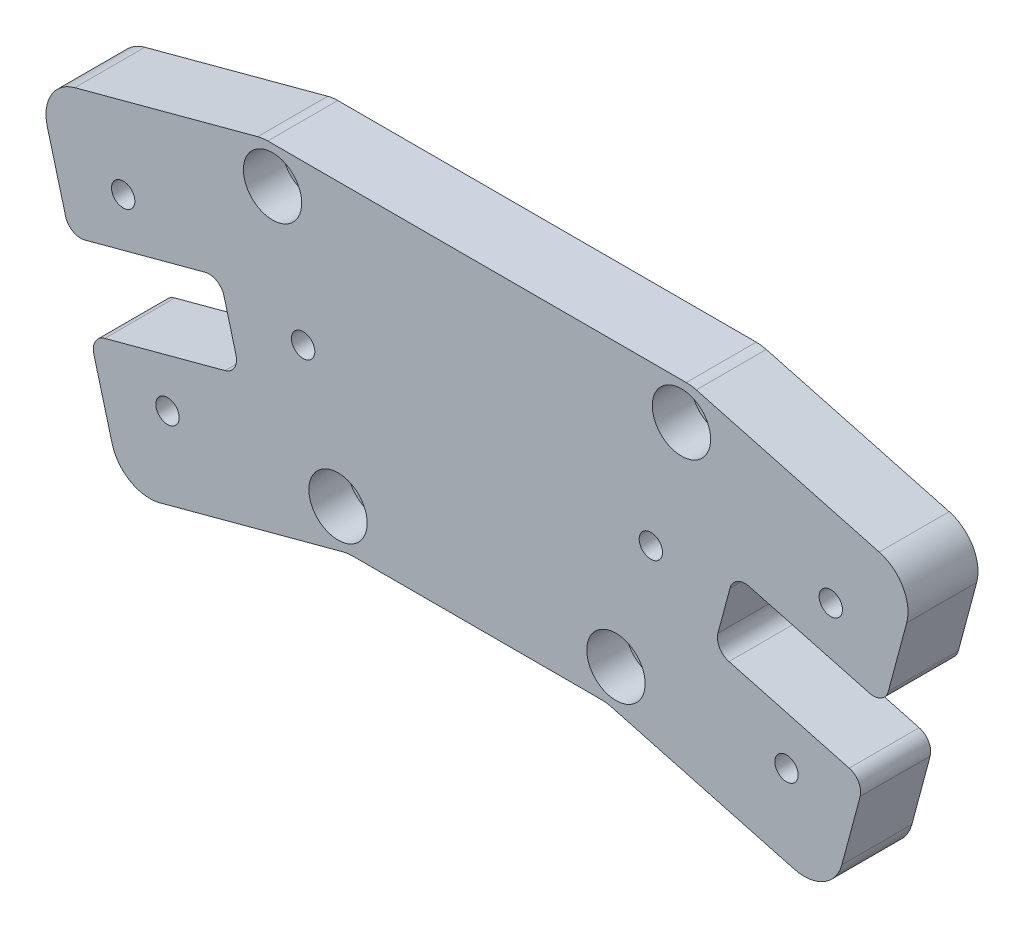
SolidWorks part; units mm, degrees
material "ABS"
ref_plane "前视基准面" through (0, 0, 0) normal (0, 0, 1) x (1, 0, 0)
ref_plane "上视基准面" through (0, 0, 0) normal (0, 1, 0) x (1, 0, 0)
ref_plane "右视基准面" through (0, 0, 0) normal (1, 0, 0) x (0, 0, -1)
other "Configuration Table"
sketch "草图1" plane through (0, 0, 0) normal (0, 0, 1) x (1, 0, 0)
  line L0 (-27.5552, 0) -> (27.5552, 0)
  line L4 (16.6342, -40.7579) -> (-16.6342, -40.7579)
  line L8 (0, 0) -> (0, -40.7579) construction
  line L9 (-45.612, -48.5224) -> (-16.6342, -40.7579)
  line L10 (-56.533, -7.7646) -> (-52.3666, -23.3139)
  line L11 (-27.5552, 0) -> (-56.533, -7.7646)
  line L12 (-60, -30.6224) -> (-60, 11.8776) construction
  line L13 (-60, -30.6224) -> (-85.8724, 3.0952) construction
  line L14 (-60, -30.6224) -> (-17.5, -30.6224) construction
  line L15 (-60, -30.6224) -> (-34.1276, -64.3399) construction
  line L16 (-27.5552, 0) -> (-16.6342, -40.7579) construction
  line L17 (-60.0552, -30.5504) -> (-22.0947, -20.3789) construction
  line L18 (-52.3666, -23.3139) -> (-33.0481, -18.1375)
  line L19 (-52.8305, -11.0149) -> (-44.0307, -43.8563) construction
  line L20 (-49.7784, -32.9731) -> (-30.4599, -27.7968)
  line L27 (-33.0481, -18.1375) -> (-30.4599, -27.7968)
  line L30 (-49.7784, -32.9731) -> (-45.612, -48.5224)
  line L31 (27.5552, 0) -> (56.533, -7.7646)
  line L32 (56.533, -7.7646) -> (52.3666, -23.3139)
  line L33 (52.3666, -23.3139) -> (33.0481, -18.1375)
  line L38 (33.0481, -18.1375) -> (30.4599, -27.7968)
  line L43 (49.7784, -32.9731) -> (30.4599, -27.7968)
  line L44 (49.7784, -32.9731) -> (45.612, -48.5224)
  line L45 (45.612, -48.5224) -> (16.6342, -40.7579)
  line L46 (-52.8305, -11.0149) -> (-45.1031, -8.9443) construction
  line L47 (-45.1031, -8.9443) -> (-18.815, -14.3238) construction
  line L48 (-18.815, -14.3238) -> (-16.2269, -23.983) construction
  line L49 (-17.5209, -19.1534) -> (-22.0947, -20.3789) construction
  line L50 (-44.0307, -43.8563) -> (-36.3032, -41.7858) construction
  line L51 (-36.3032, -41.7858) -> (-16.2269, -23.983) construction
  line L52 (-45.482, -15.2575) -> (-39.788, -36.5079) construction
  circle A0 centre (-60, -30.6224) radius 42.5 construction
  circle A1 centre (-85.8724, 3.0952) radius 1.75 construction
  circle A2 centre (-54.4526, 11.514) radius 1.75 construction
  circle A3 centre (-26.2825, -4.75) radius 1.75
  circle A4 centre (-17.8636, -36.1697) radius 1.75
  circle A5 centre (-34.1276, -64.3399) radius 1.75 construction
  circle A6 centre (-65.5474, -72.7588) radius 1.75 construction
  circle A7 centre (-93.7175, -56.4947) radius 1.75 construction
  circle A8 centre (-102.1364, -25.075) radius 1.75 construction
  circle A9 centre (-26.2825, -4.75) radius 3.75 construction
  circle A11 centre (-17.8636, -36.1697) radius 3.75 construction
  circle A12 centre (-26.2825, -4.75) radius 4.75 construction
  circle A13 centre (-17.8636, -36.1697) radius 4.75 construction
  circle A14 centre (17.8636, -36.1697) radius 1.75
  circle A15 centre (26.2825, -4.75) radius 1.75
  circle A16 centre (60, -30.6224) radius 42.5 construction
  circle A17 centre (-45.482, -15.2575) radius 1.5
  circle A18 centre (-22.3506, -20.4475) radius 1.5
  circle A19 centre (-39.788, -36.5079) radius 1.5
  circle A20 centre (45.482, -15.2575) radius 1.5
  circle A21 centre (39.788, -36.5079) radius 1.5
  circle A22 centre (22.3506, -20.4475) radius 1.5
  point P31 (-60, -30.6224)
  point P45 (-48.4306, -27.4356)
  dimension "D6" = 85
  dimension "D9" = 3.5
  dimension "D10" = 7.5
  dimension "D14" = 1
  dimension "D4" = 1
  dimension "D12" = 12
  dimension "D19" = 22
  dimension "D20" = 3
  dimension "D21" = 5
  dimension "D2" = 120
  dimension "D3" = 10
  dimension "D5" = 30
  dimension "D7" = 37.5
  dimension "D11" = 20
  dimension "D13" = 8
  dimension "D15" = 10
  dimension "D16" = 32
  dimension "D17" = 34
  dimension "D18" = 6
  dimension "D8" = 8
extrude "凸台-拉伸1" add sketch "草图1" along normal blind 9 contours L0 L31 L32 L33 L38 L43 L44 L45 L4 L9 L30 L20 L27 L18 L10 L11
fillet "圆角1" radius 5 8 edges at (27.5552, 0, 4.5) (56.533, -7.7646, 4.5) (16.6342, -40.7579, 4.5) (45.612, -48.5224, 4.5) (-45.612, -48.5224, 4.5) (-16.6342, -40.7579, 4.5) (-27.5552, 0, 4.5) (-56.533, -7.7646, 4.5)
sketch "草图2" plane through (0, 0, 0) normal (0, 0, -1) x (-1, 0, 0)
  line L0 (-45.482, -15.2575) -> (-22.3506, -20.4475) construction
  line L1 (-42.3033, -14.4058) -> (-44.6303, -12.0787)
  line L2 (-44.6303, -12.0787) -> (-47.809, -12.9305)
  line L3 (-47.809, -12.9305) -> (-48.6608, -16.1093)
  line L4 (-48.6608, -16.1093) -> (-46.3338, -18.4363)
  line L5 (-46.3338, -18.4363) -> (-43.155, -17.5845)
  line L6 (-43.155, -17.5845) -> (-42.3033, -14.4058)
  line L7 (-22.3506, -20.4475) -> (-39.788, -36.5079) construction
  line L8 (-39.788, -36.5079) -> (-45.482, -15.2575) construction
  line L9 (-30.4599, -27.7968) -> (-33.0481, -18.1375) construction
  line L10 (-31.754, -22.9671) -> (-22.3506, -20.4475) construction
  line L11 (-33.0481, -18.1375) -> (-52.3666, -23.3139) construction
  line L12 (0, 0) -> (0, -40.7579) construction
  line L13 (-21.4988, -23.6263) -> (-19.1718, -21.2992)
  line L14 (-19.1718, -21.2992) -> (-20.0236, -18.1205)
  line L15 (-20.0236, -18.1205) -> (-23.2023, -17.2687)
  line L16 (-23.2023, -17.2687) -> (-25.5293, -19.5957)
  line L17 (-25.5293, -19.5957) -> (-24.6776, -22.7745)
  line L18 (-24.6776, -22.7745) -> (-21.4988, -23.6263)
  line L19 (-36.6092, -35.6561) -> (-38.9363, -33.3291)
  line L20 (-38.9363, -33.3291) -> (-42.115, -34.1809)
  line L21 (-42.115, -34.1809) -> (-42.9668, -37.3596)
  line L22 (-42.9668, -37.3596) -> (-40.6398, -39.6866)
  line L23 (-40.6398, -39.6866) -> (-37.461, -38.8349)
  line L24 (-37.461, -38.8349) -> (-36.6092, -35.6561)
  line L25 (15.9759, -40.7579) -> (-15.9759, -40.7579) construction
  line L26 (37.461, -38.8349) -> (36.6092, -35.6561)
  line L27 (40.6398, -39.6866) -> (37.461, -38.8349)
  line L28 (42.9668, -37.3596) -> (40.6398, -39.6866)
  line L29 (42.115, -34.1809) -> (42.9668, -37.3596)
  line L30 (38.9363, -33.3291) -> (42.115, -34.1809)
  line L31 (36.6092, -35.6561) -> (38.9363, -33.3291)
  line L32 (43.155, -17.5845) -> (42.3033, -14.4058)
  line L33 (46.3338, -18.4363) -> (43.155, -17.5845)
  line L34 (48.6608, -16.1093) -> (46.3338, -18.4363)
  line L35 (47.809, -12.9305) -> (48.6608, -16.1093)
  line L36 (44.6303, -12.0787) -> (47.809, -12.9305)
  line L37 (42.3033, -14.4058) -> (44.6303, -12.0787)
  line L38 (24.6776, -22.7745) -> (21.4988, -23.6263)
  line L39 (25.5293, -19.5957) -> (24.6776, -22.7745)
  line L40 (23.2023, -17.2687) -> (25.5293, -19.5957)
  line L41 (20.0236, -18.1205) -> (23.2023, -17.2687)
  line L42 (19.1718, -21.2992) -> (20.0236, -18.1205)
  line L43 (21.4988, -23.6263) -> (19.1718, -21.2992)
  circle A0 centre (-45.482, -15.2575) radius 2.85 construction
  circle A1 centre (-22.3506, -20.4475) radius 2.85 construction
  circle A2 centre (-39.788, -36.5079) radius 2.85 construction
  circle A6 centre (-22.3506, -20.4475) radius 1.5 construction
  circle A8 centre (-45.482, -15.2575) radius 1.5 construction
  dimension "D1" = 5.7
extrude "切除-拉伸1" cut sketch "草图2" against normal blind 3.5
sketch "草图5" plane through (0, 0, 9) normal (0, 0, 1) x (1, 0, 0)
  circle A0 centre (-26.2825, -4.75) radius 3.75
  circle A1 centre (-17.8636, -36.1697) radius 3.75
  circle A2 centre (17.8636, -36.1697) radius 3.75
  circle A3 centre (26.2825, -4.75) radius 3.75
  dimension "D1" = 7.5
extrude "切除-拉伸2" cut sketch "草图5" against normal offset from surface (5 mm away) 4 up to face at (39.788, -36.5079, 0)
fillet "圆角2" radius 2 8 edges at (49.7784, -32.9731, 4.5) (52.3666, -23.3139, 4.5) (30.4599, -27.7968, 4.5) (33.0481, -18.1375, 4.5) (-49.7784, -32.9731, 4.5) (-30.4599, -27.7968, 4.5) (-52.3666, -23.3139, 4.5) (-33.0481, -18.1375, 4.5)
